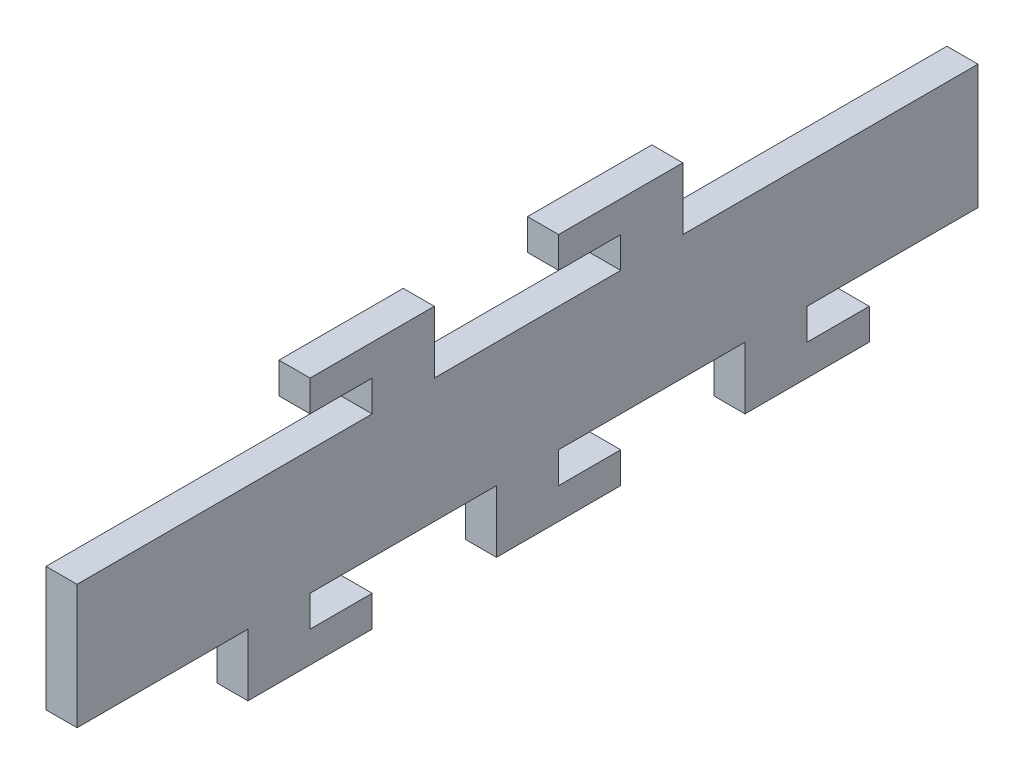
SolidWorks part; units mm, degrees
ref_plane "Plan de face" through (0, 0, 0) normal (0, 0, 1) x (1, 0, 0)
ref_plane "Plan de dessus" through (0, 0, 0) normal (0, 1, 0) x (1, 0, 0)
ref_plane "Plan de droite" through (0, 0, 0) normal (1, 0, 0) x (0, 0, -1)
sketch "Esquisse1" plane through (0, 0, 0) normal (1, 0, 0) x (0, 0, -1)
  line L0 (72.5, -10) -> (45, -10)
  line L1 (-72.5, 10) -> (72.5, 10) construction
  line L2 (-72.5, 10) -> (-72.5, -10)
  line L3 (-72.5, -10) -> (72.5, -10) construction
  line L4 (72.5, 10) -> (72.5, -10)
  line L5 (45, -10) -> (45, -15)
  line L6 (45, -15) -> (55, -15)
  line L7 (55, -15) -> (55, -20)
  line L8 (55, -20) -> (35, -20)
  line L9 (35, -20) -> (35, -10)
  line L10 (35, -10) -> (5, -10)
  line L11 (5, -10) -> (5, -15)
  line L12 (5, -15) -> (15, -15)
  line L13 (15, -15) -> (15, -20)
  line L14 (15, -20) -> (-5, -20)
  line L15 (-5, -20) -> (-5, -10)
  line L16 (-5, -10) -> (-35, -10)
  line L17 (-35, -10) -> (-35, -15)
  line L18 (-35, -15) -> (-25, -15)
  line L19 (-25, -15) -> (-25, -20)
  line L20 (-25, -20) -> (-45, -20)
  line L21 (-45, -20) -> (-45, -10)
  line L22 (-72.5, -10) -> (-45, -10)
  line L23 (-72.5, 10) -> (-25, 10)
  line L30 (-25, 10) -> (-25, 15)
  line L31 (-25, 15) -> (-35, 15)
  line L32 (-35, 15) -> (-35, 20)
  line L33 (-35, 20) -> (-15, 20)
  line L34 (-15, 20) -> (-15, 10)
  line L35 (-15, 10) -> (15, 10)
  line L36 (15, 10) -> (15, 15)
  line L37 (15, 15) -> (5, 15)
  line L38 (5, 15) -> (5, 20)
  line L39 (5, 20) -> (25, 20)
  line L40 (25, 20) -> (25, 10)
  line L41 (25, 10) -> (72.5, 10)
  dimension "D1" = 145
  dimension "D2" = 72.5
  dimension "D3" = 20
  dimension "D4" = 10
  dimension "D5" = 27.5
  dimension "D6" = 10
  dimension "D7" = 5
  dimension "D8" = 5
  dimension "D9" = 20
  dimension "D10" = 30
  dimension "D11" = 10
  dimension "D12" = 5
  dimension "D13" = 5
  dimension "D14" = 20
  dimension "D15" = 30
  dimension "D16" = 10
  dimension "D17" = 5
  dimension "D18" = 5
  dimension "D19" = 20
  dimension "D20" = 25
  dimension "D26" = 5
  dimension "D27" = 10
  dimension "D28" = 5
  dimension "D29" = 20
  dimension "D30" = 5
  dimension "D31" = 10
  dimension "D32" = 5
  dimension "D33" = 20
  dimension "D34" = 30
extrude "Boss.-Extru.1" add sketch "Esquisse1" along normal blind 5
